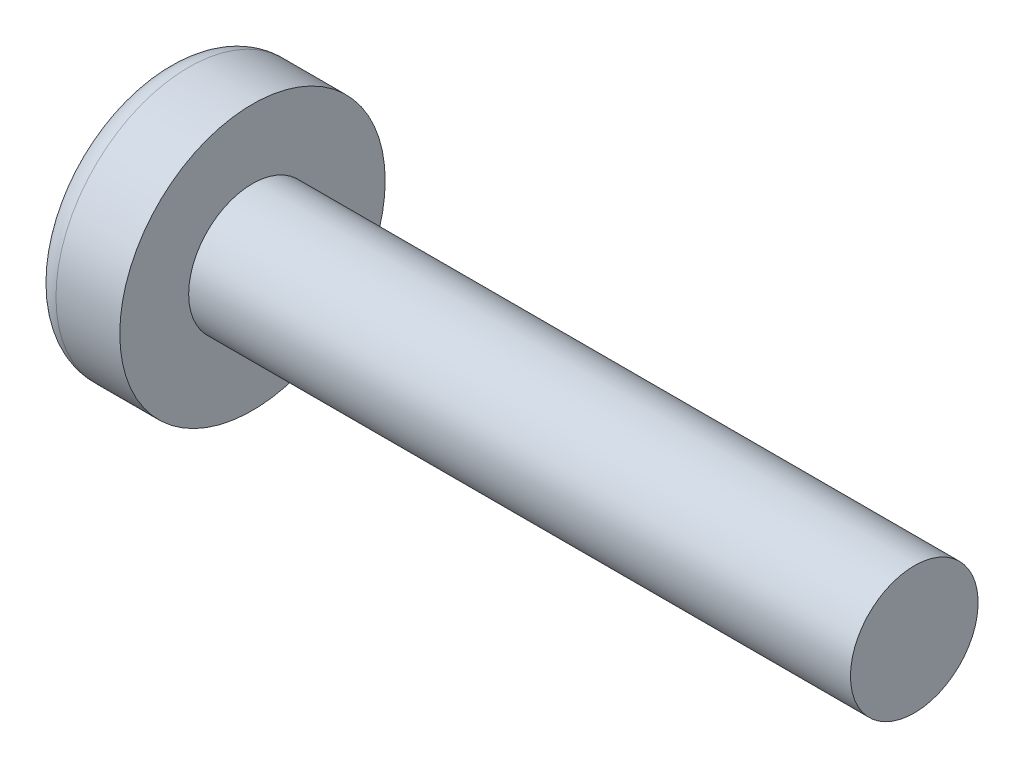
SolidWorks part; units mm, degrees
ref_plane "Plane1" through (0, 0, 0) normal (0, 0, 1) x (1, 0, 0)
ref_plane "Plane2" through (0, 0, 0) normal (0, 1, 0) x (1, 0, 0)
ref_plane "Plane3" through (0, 0, 0) normal (1, 0, 0) x (0, 0, -1)
sketch "BodySke" plane through (0, 0, 0) normal (0, 0, 1) x (1, 0, 0)
  line L0 (1.6, 0.95) -> (1.6, 1.975)
  line L1 (2.1, 6.35) -> (2.1, -3.175) construction
  line L2 (-25.4, 0) -> (127, 0) construction
  line L3 (11.45, 0) -> (0, 0)
  line L4 (1.6, 0.95) -> (11.45, 0.95)
  line L5 (11.45, 0.95) -> (11.45, 0)
  line L6 (0.6501, 1.975) -> (1.6, 1.975)
  line L7 (1.6, -0.95) -> (11.45, -0.95) construction
  line L8 (1.6, 6.35) -> (1.6, -3.175) construction
  arc A0 (0.3126, 1.7403) -> (0, 0) centre (5, 0) ccw
  arc A2 (0.3126, 1.7403) -> (0.6501, 1.975) centre (0.6501, 1.615) cw
  dimension "Head_crown_rad" = 5
  dimension "Head_fillet_rad" = 0.36
  dimension "Diameter" = 1.9
  dimension "Length" = 9.85
  dimension "Head_ht" = 1.6
  dimension "Head_dia" = 3.95
  dimension "Advance" = 0.5
  dimension "Thread_nom" = 9.85
revolve "Base-Revolve" add sketch "BodySke" angle 360 about L2
cosmetic thread "ThreadCosmetic" [suppressed] parameters "Thread_length"=9.35, "Thread_minor"=2.439
sketch "Sketch3" plane through (0, 0, 0) normal (1, 0, 0) x (0, 0, -1)
  line L0 (0.37, -1.45) -> (-0.37, -1.45)
  line L1 (0.37, -1.45) -> (0.37, 1.45)
  line L2 (-0.37, 1.45) -> (0.37, 1.45)
  line L3 (-0.37, 1.45) -> (-0.37, -1.45)
  dimension "Cross_dia" = 2.9
  dimension "D1" = 1.45
  dimension "Cross_width" = 0.74
  dimension "D2" = 0.37
ref_plane "Plane4" through (1.76, 0, 0) normal (1, 0, 0) x (0, 0, -1)
sketch "Sketch4" plane through (1.76, 0, 0) normal (1, 0, 0) x (0, 0, -1)
  line L0 (0.185, -0.185) -> (-0.185, -0.185)
  line L1 (0.185, -0.185) -> (0.185, 0.185)
  line L2 (-0.185, 0.185) -> (0.185, 0.185)
  line L3 (-0.185, 0.185) -> (-0.185, -0.185)
  dimension "D2" = 0.37
  dimension "D1" = 0.37
  dimension "D3" = 0.185
  dimension "D4" = 0.185
loft "Cut-Loft1" cut profiles "Sketch3", "Sketch4"
pattern_circular "CirPattern1" count 2 every 90 about axis through (0, 0, 0) along (1, 0, 0) of "Cut-Loft1"
sketch "ThdSchSke" plane through (0, 0, 0) normal (0, 0, 1) x (1, 0, 0)
  line L0 (2.1, -1.2195) -> (2.2887, -0.95)
  line L1 (2.1, -1.2195) -> (1.9113, -0.95)
  line L2 (1.9113, -0.95) -> (1.9113, -1.1875)
  line L3 (-3.175, 0) -> (5.1513, 0) construction
  line L5 (1.9113, -1.1875) -> (2.2887, -1.1875)
  line L6 (2.2887, -1.1875) -> (2.2887, -0.95)
  dimension "Diameter" = 1.9
  dimension "SideAngle" = 55
  dimension "VeeAngle" = 70
  dimension "Thread_minor" = 2.439
  dimension "Overcut" = 2.375
  dimension "Start" = 2.1
revolve "ThreadSchematic" [suppressed] cut sketch "ThdSchSke" angle 360 about L3
pattern_linear "ThdSchPat" [suppressed]
equation "\"D1@Sketch3\" = \"Cross_dia@Sketch3\" / 2"
equation "\"D2@Sketch3\" = \"Cross_width@Sketch3\" / 2"
equation "\"D1@Sketch4\" = \"Cross_width@Sketch3\" *.5"
equation "\"D2@Sketch4\" = \"D1@Sketch4\""
equation "\"D3@Sketch4\" = \"D1@Sketch4\" / 2"
equation "\"D4@Sketch4\" = \"D2@Sketch4\" / 2"
equation "\"Thread_length@ThreadCosmetic\" = ((sgn( (\"Length@BodySke\" - \"Advance@BodySke\" ) - \"Thread_nom@BodySke\" )-1)*( (\"Length@BodySke\" - \"Advance@BodySke\" ) - \"Thread_nom@BodySke\" ))/-2+ \"Thread_nom@BodySke\""
equation "\"Thread_minor@ThdSchSke\" = \"Thread_minor@ThreadCosmetic\""
equation "\"Diameter@ThdSchSke\" = \"Diameter@BodySke\""
equation "\"Overcut@ThdSchSke\" = \"Diameter@BodySke\" * 1.25"
equation "\"Start@ThdSchSke\" = \"Head_ht@BodySke\" + \"Length@BodySke\" - \"Thread_length@ThreadCosmetic\"  '---Non-countersunk---"
equation "\"Num_threads@ThdSchPat\" = int( \"Thread_length@ThreadCosmetic\" / \"Advance@BodySke\" + 0.999 )  + 1"
equation "\"Advance@ThdSchPat\" = \"Thread_length@ThreadCosmetic\" /  (\"Num_threads@ThdSchPat\" - 1) 'relax it"
